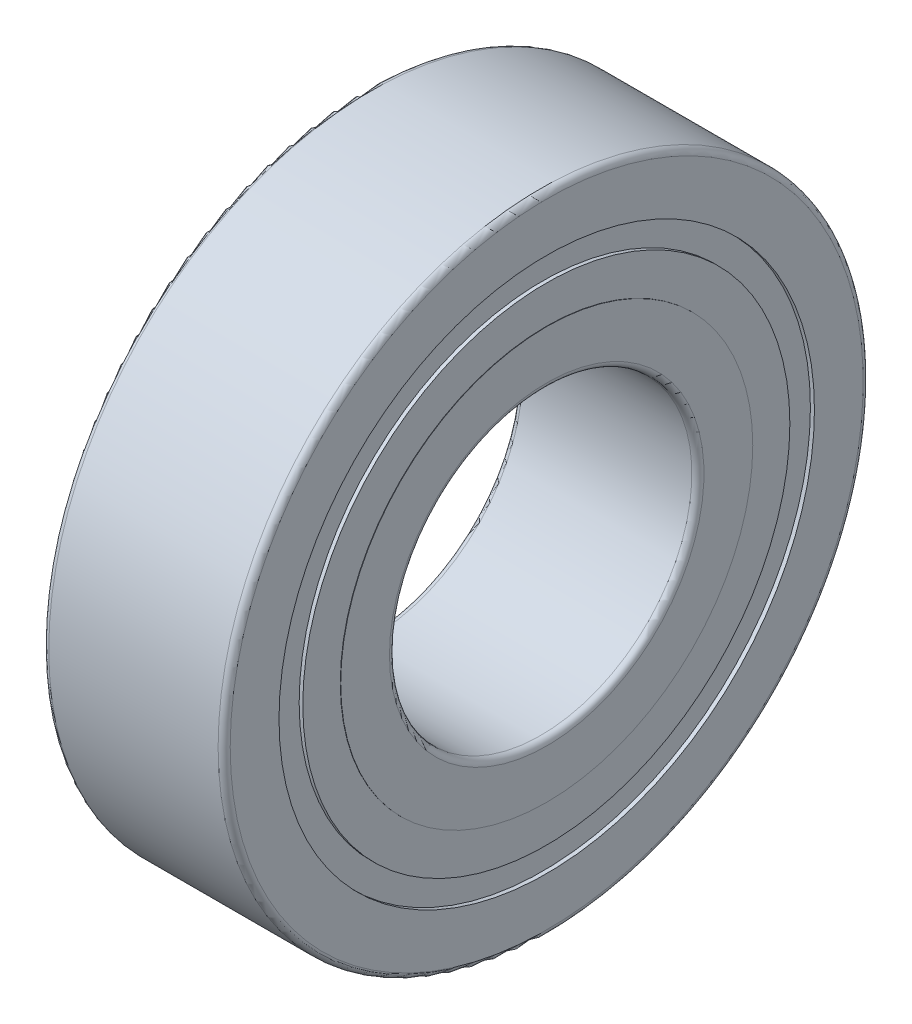
SolidWorks part; units mm, degrees
ref_plane "Front Plane" through (0, 0, 0) normal (0, 0, 1) x (1, 0, 0)
ref_plane "Top Plane" through (0, 0, 0) normal (0, 1, 0) x (1, 0, 0)
ref_plane "Right Plane" through (0, 0, 0) normal (1, 0, 0) x (0, 0, -1)
ref_plane "Plane1" through (0, 0, 0) normal (0, 0, 1) x (1, 0, 0)
sketch "Sketch1" plane through (0, 0, 0) normal (0, 0, 1) x (1, 0, 0)
  line L0 (-4.5, 15.7) -> (-4.5, 7.8)
  line L1 (-4.2, 7.5) -> (4.2, 7.5)
  line L2 (4.5, 7.8) -> (4.5, 15.7)
  line L3 (4.2, 16) -> (-4.2, 16)
  line L4 (50, 0) -> (-50, 0) construction
  arc A0 (-4.5, 7.8) -> (-4.2, 7.5) centre (-4.2, 7.8) ccw
  arc A1 (4.2, 7.5) -> (4.5, 7.8) centre (4.2, 7.8) ccw
  arc A2 (4.5, 15.7) -> (4.2, 16) centre (4.2, 15.7) ccw
  arc A3 (-4.2, 16) -> (-4.5, 15.7) centre (-4.2, 15.7) ccw
revolve "Revolve1" add sketch "Sketch1" angle 360 about L4
ref_plane "Plane2" through (0, 0, 0) normal (0, 0, 1) x (1, 0, 0)
sketch "Sketch2" plane through (0, 0, 0) normal (0, 0, 1) x (1, 0, 0)
  line L0 (-6.3, 7.5) -> (-4.5, 7.5)
  line L1 (-4.5, 7.5) -> (-4.5, 10.22)
  line L2 (-4.5, 10.22) -> (-4.48, 10.22)
  line L3 (-4.48, 10.22) -> (-4.48, 12.08)
  line L4 (-4.48, 12.08) -> (-4.3, 12.08)
  line L5 (-4.3, 12.08) -> (-4.3, 13.28)
  line L6 (-4.3, 13.28) -> (-6.3, 13.28)
  line L7 (-6.3, 13.28) -> (-6.3, 7.5)
  line L8 (50, 0) -> (-50, 0) construction
revolve "Cut-Revolve1" cut sketch "Sketch2" angle 360 about L8
ref_plane "Plane3" through (0, 0, 0) normal (0, 0, 1) x (1, 0, 0)
sketch "Sketch3" plane through (0, 0, 0) normal (0, 0, 1) x (1, 0, 0)
  line L0 (4.3, 13.28) -> (4.3, 12.08)
  line L1 (4.3, 12.08) -> (4.48, 12.08)
  line L2 (4.48, 12.08) -> (4.48, 10.22)
  line L3 (4.48, 10.22) -> (4.5, 10.22)
  line L4 (4.5, 10.22) -> (4.5, 7.5)
  line L5 (4.5, 7.5) -> (6.3, 7.5)
  line L6 (6.3, 7.5) -> (6.3, 13.28)
  line L7 (6.3, 13.28) -> (4.3, 13.28)
  line L8 (50, 0) -> (-50, 0) construction
revolve "Cut-Revolve2" cut sketch "Sketch3" angle 360 about L8
scale "Scale1" scale about centroid uniform scaling yes scale factor 3.2
